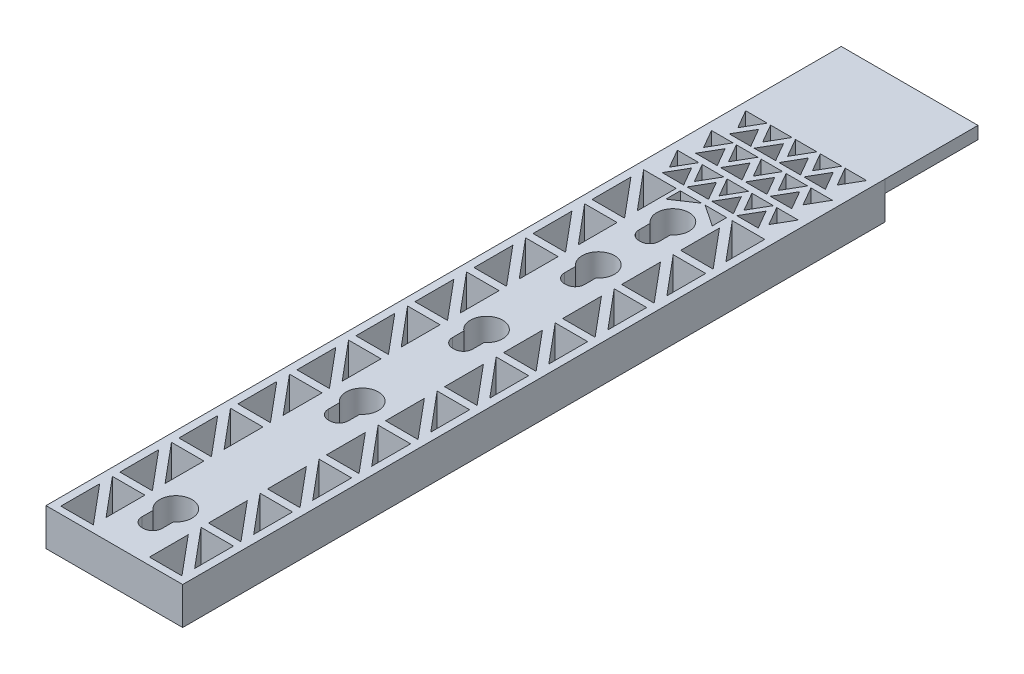
SolidWorks part; units mm, degrees
ref_plane "Front Plane" through (0, 0, 0) normal (0, 0, 1) x (1, 0, 0)
ref_plane "Top Plane" through (0, 0, 0) normal (0, 1, 0) x (1, 0, 0)
ref_plane "Right Plane" through (0, 0, 0) normal (1, 0, 0) x (0, 0, -1)
sketch "Sketch23" plane through (0, 0, 0) normal (0, 1, 0) x (1, 0, 0)
  line L1 (181.0964, 0) -> (203.0964, 0)
  line L2 (181.0964, 0) -> (181.0964, -113)
  line L3 (181.0964, -113) -> (203.0964, -113)
  line L4 (203.0964, 0) -> (203.0964, -113)
  circle A0 centre (192, -73) radius 2.6
  circle A1 centre (192, -53) radius 2.6
  circle A2 centre (192, -35) radius 2.6
  circle A3 centre (192, -23) radius 2.6
  circle A4 centre (192, -103) radius 2.6
  dimension "D1" = 10
  dimension "D8" = 5.2
  dimension "D9" = 5.2
  dimension "D10" = 5.2
  dimension "D11" = 5.2
  dimension "D12" = 5.2
  dimension "D2" = 30
  dimension "D3" = 20
  dimension "D4" = 18
  dimension "D5" = 12
  dimension "D6" = 22
  dimension "D7" = 113
extrude "Boss-Extrude3" add sketch "Sketch23" against normal blind 6
sketch "Sketch25" plane through (0, 0, 0) normal (0, 1, 0) x (1, 0, 0)
  line L1 (190.375, -108.35) -> (193.625, -108.35)
  line L2 (190.375, -108.35) -> (190.375, -102.85)
  line L3 (190.375, -102.85) -> (193.625, -102.85)
  line L4 (193.625, -108.35) -> (193.625, -102.85)
  line L5 (190.375, -108.35) -> (193.625, -102.85) construction
  line L6 (190.375, -102.85) -> (193.625, -108.35) construction
  line L7 (190.375, -78.35) -> (193.625, -78.35)
  line L8 (190.375, -78.35) -> (190.375, -72.85)
  line L9 (190.375, -72.85) -> (193.625, -72.85)
  line L10 (193.625, -78.35) -> (193.625, -72.85)
  line L11 (190.375, -78.35) -> (193.625, -72.85) construction
  line L12 (190.375, -72.85) -> (193.625, -78.35) construction
  line L13 (190.375, -58.35) -> (193.625, -58.35)
  line L14 (190.375, -58.35) -> (190.375, -52.85)
  line L15 (190.375, -52.85) -> (193.625, -52.85)
  line L16 (193.625, -58.35) -> (193.625, -52.85)
  line L17 (190.375, -58.35) -> (193.625, -52.85) construction
  line L18 (190.375, -52.85) -> (193.625, -58.35) construction
  line L19 (190.375, -40.35) -> (193.625, -40.35)
  line L20 (190.375, -40.35) -> (190.375, -34.85)
  line L21 (190.375, -34.85) -> (193.625, -34.85)
  line L22 (193.625, -40.35) -> (193.625, -34.85)
  line L23 (190.375, -40.35) -> (193.625, -34.85) construction
  line L24 (190.375, -34.85) -> (193.625, -40.35) construction
  line L25 (190.375, -28.35) -> (193.625, -28.35)
  line L26 (190.375, -28.35) -> (190.375, -22.85)
  line L27 (190.375, -22.85) -> (193.625, -22.85)
  line L28 (193.625, -28.35) -> (193.625, -22.85)
  line L29 (190.375, -28.35) -> (193.625, -22.85) construction
  line L30 (190.375, -22.85) -> (193.625, -28.35) construction
  circle A0 centre (192, -103) radius 2.6 construction
  circle A1 centre (192, -73) radius 2.6 construction
  circle A2 centre (192, -53) radius 2.6 construction
  circle A3 centre (192, -35) radius 2.6 construction
  circle A4 centre (192, -23) radius 2.6 construction
  point P0 (192, -105.6)
  point P7 (192, -75.6)
  point P14 (192, -55.6)
  point P22 (192, -37.6)
  point P29 (192, -25.6)
extrude "Cut-Extrude1" cut sketch "Sketch25" against normal blind 15.322
fillet "Fillet1" radius 1.5 8 edges at (193.625, -3, 108.35) (190.375, -3, 108.35) (193.625, -3, 78.35) (190.375, -3, 78.35) (193.625, -3, 40.35) (190.375, -3, 40.35) (190.375, -3, 28.35) (193.625, -3, 28.35)
fillet "Fillet2" radius 1.5 2 edges at (190.375, -3, 58.35) (193.625, -3, 58.35)
sketch "Sketch30" plane through (0, 0, 0) normal (0, 1, 0) x (1, 0, 0)
  line L1 (192.0964, -4.6548) -> (193.8285, -1.6548)
  line L2 (193.8285, -1.6548) -> (190.3644, -1.6548)
  line L3 (190.3644, -1.6548) -> (192.0964, -4.6548)
  circle A0 centre (192.0964, -2.6548) radius 1 construction
  dimension "D1" = 11
extrude "Cut-Extrude7" cut sketch "Sketch30" against normal blind 13.7948
pattern_linear "LPattern3" count 3 spacing 4 along (-1, 0, 0) count 3 spacing 4 along (1, 0, 0) of "Cut-Extrude7"
pattern_linear "LPattern4" count 3 spacing 5.5 along (0, 0, 1) of "LPattern3", "Cut-Extrude7"
sketch "Sketch31" plane through (0, 0, 0) normal (0, 1, 0) x (1, 0, 0)
  line L1 (185.9964, -3.2) -> (184.2644, -6.2)
  line L2 (184.2644, -6.2) -> (187.7285, -6.2)
  line L3 (187.7285, -6.2) -> (185.9964, -3.2)
  circle A0 centre (185.9964, -5.2) radius 1 construction
  dimension "D1" = 4.9
  dimension "D2" = 5.2
extrude "Cut-Extrude8" cut sketch "Sketch31" against normal blind 13.4849
pattern_linear "LPattern5" count 4 spacing 4 along (1, 0, 0) count 3 spacing 5.4 along (0, 0, 1) of "Cut-Extrude8"
sketch "Sketch33" plane through (0, 0, 0) normal (0, 1, 0) x (1, 0, 0)
  line L0 (201.8264, -18.05) -> (196.5964, -18.05)
  line L1 (196.5964, -18.05) -> (201.8264, -24.3028)
  line L2 (201.8264, -24.3028) -> (201.8264, -18.05)
  dimension "D1" = 1.27
  dimension "D2" = 1.05
  dimension "D3" = 6.5
extrude "Cut-Extrude9" cut sketch "Sketch33" against normal blind 53.6723
pattern_linear "LPattern7" count 10 spacing 9.5 along (0, 0, 1) of "Cut-Extrude9"
sketch "Sketch38" plane through (0, 0, 0) normal (0, 1, 0) x (1, 0, 0)
  line L0 (187.5964, -18.08) -> (182.3664, -18.08)
  line L1 (182.3664, -18.08) -> (187.5964, -24.3328)
  line L2 (187.5964, -24.3328) -> (187.5964, -18.08)
  dimension "D1" = 1.27
  dimension "D2" = 1.08
extrude "Cut-Extrude10" cut sketch "Sketch38" against normal blind 24.8037
pattern_linear "LPattern8" count 10 spacing 9.5 along (0, 0, 1) of "Cut-Extrude10"
sketch "Sketch39" plane through (0, 0, 0) normal (0, 1, 0) x (1, 0, 0)
  line L0 (201.8264, -26.35) -> (196.5964, -20.1)
  line L1 (196.5964, -20.1) -> (196.5964, -26.35)
  line L2 (196.5964, -26.35) -> (201.8264, -26.35)
  dimension "D1" = 1.27
  dimension "D2" = 5.23
  dimension "D3" = 1.2
  dimension "D4" = 2.05
extrude "Cut-Extrude11" cut sketch "Sketch39" against normal blind 27.4066
pattern_linear "LPattern9" count 10 spacing 9.5 along (0, 0, 1) of "Cut-Extrude11"
sketch "Sketch40" plane through (0, 0, 0) normal (0, 1, 0) x (1, 0, 0)
  line L0 (187.5964, -26.38) -> (182.3664, -20.13)
  line L1 (182.3664, -20.13) -> (182.3664, -26.38)
  line L2 (182.3664, -26.38) -> (187.5964, -26.38)
  dimension "D1" = 1.27
  dimension "D2" = 2.05
extrude "Cut-Extrude12" cut sketch "Sketch40" against normal blind 18.7522
pattern_linear "LPattern10" count 10 spacing 9.5 along (0, 0, 1) of "Cut-Extrude12"
sketch "Sketch41" plane through (0, 0, 0) normal (0, 1, 0) x (1, 0, 0)
  line L0 (188.2644, -18.08) -> (191.7285, -18.08)
  line L1 (191.7285, -18.08) -> (188.2644, -20.4)
  line L2 (188.2644, -20.4) -> (188.2644, -18.08)
  line L3 (195.7285, -18.08) -> (192.2644, -18.08)
  line L4 (192.2644, -18.08) -> (195.7285, -20.4)
  line L5 (195.7285, -20.4) -> (195.7285, -18.08)
extrude "Cut-Extrude13" cut sketch "Sketch41" against normal blind 6
sketch "Sketch42" plane through (0, 0, 0) normal (0, 1, 0) x (1, 0, 0)
  line L1 (181.0964, 0) -> (203.1, 0)
  line L2 (181.0964, 0) -> (181.0964, 15)
  line L3 (181.0964, 15) -> (203.1, 15)
  line L4 (203.1, 0) -> (203.1, 15)
extrude "Boss-Extrude4" add sketch "Sketch42" against normal blind 2
sketch "Sketch48" plane through (0, -2, 0) normal (0, -1, 0) x (1, 0, 0)
  line L1 (189.0964, -12) -> (195.1, -12)
  line L2 (189.0964, -12) -> (189.0964, -8)
  line L4 (195.1, -12) -> (195.1, -8)
  line L5 (181.0964, -15) -> (181.0964, 0) construction
  line L6 (203.1, 0) -> (203.1, -15) construction
  line L8 (186.0964, -8) -> (189.0964, -8)
  line L9 (186.0964, -8) -> (186.0964, -4)
  line L10 (186.0964, -4) -> (198.1, -4)
  line L11 (198.1, -8) -> (198.1, -4)
  line L13 (195.1, -8) -> (198.1, -8)
  line L14 (181.0964, 0) -> (203.0964, 0) construction
  dimension "D1" = 8
  dimension "D2" = 8
  dimension "D3" = 4
  dimension "D4" = 3
  dimension "D5" = 3
  dimension "D6" = 4
  dimension "D7" = 4
extrude "Boss-Extrude5" add sketch "Sketch48" along normal blind 4
